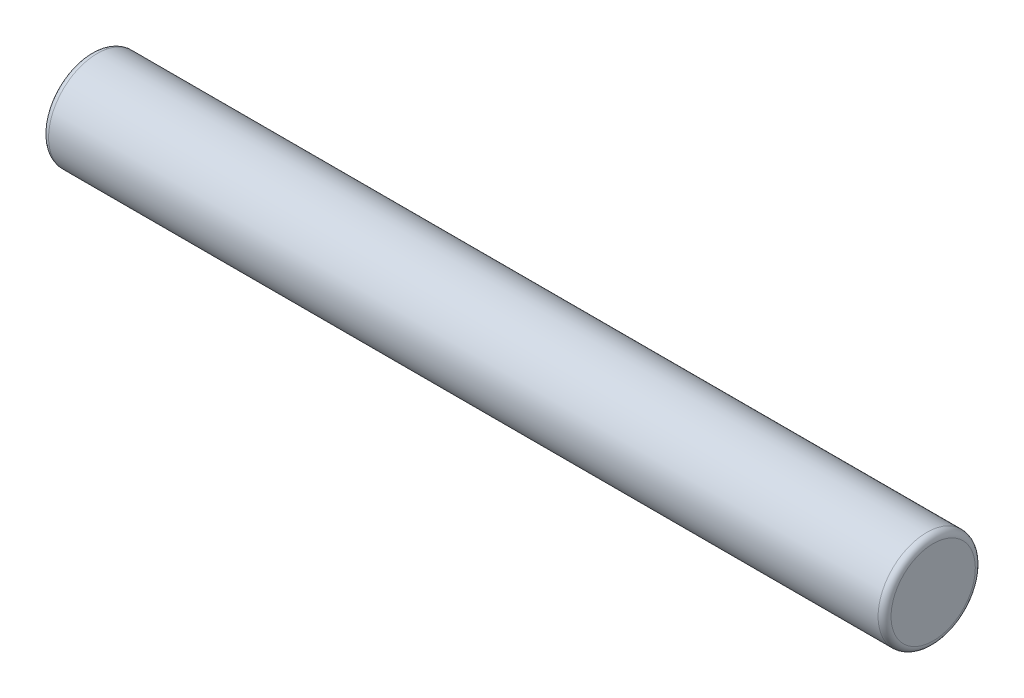
SolidWorks part; units mm, degrees
ref_plane "Front Plane" through (0, 0, 0) normal (0, 0, 1) x (1, 0, 0)
ref_plane "Top Plane" through (0, 0, 0) normal (0, 1, 0) x (1, 0, 0)
ref_plane "Right Plane" through (0, 0, 0) normal (1, 0, 0) x (0, 0, -1)
sketch "Sketch1" plane through (0, 0, 0) normal (1, 0, 0) x (0, 0, -1)
  circle A0 centre (0, 0) radius 1.5
  dimension "D1" = 3
extrude "Boss-Extrude1" add sketch "Sketch1" along normal mid plane 26
fillet "Fillet1" radius 0.2 2 edges at (-13, 0, -1.5) (13, 0, -1.5)
